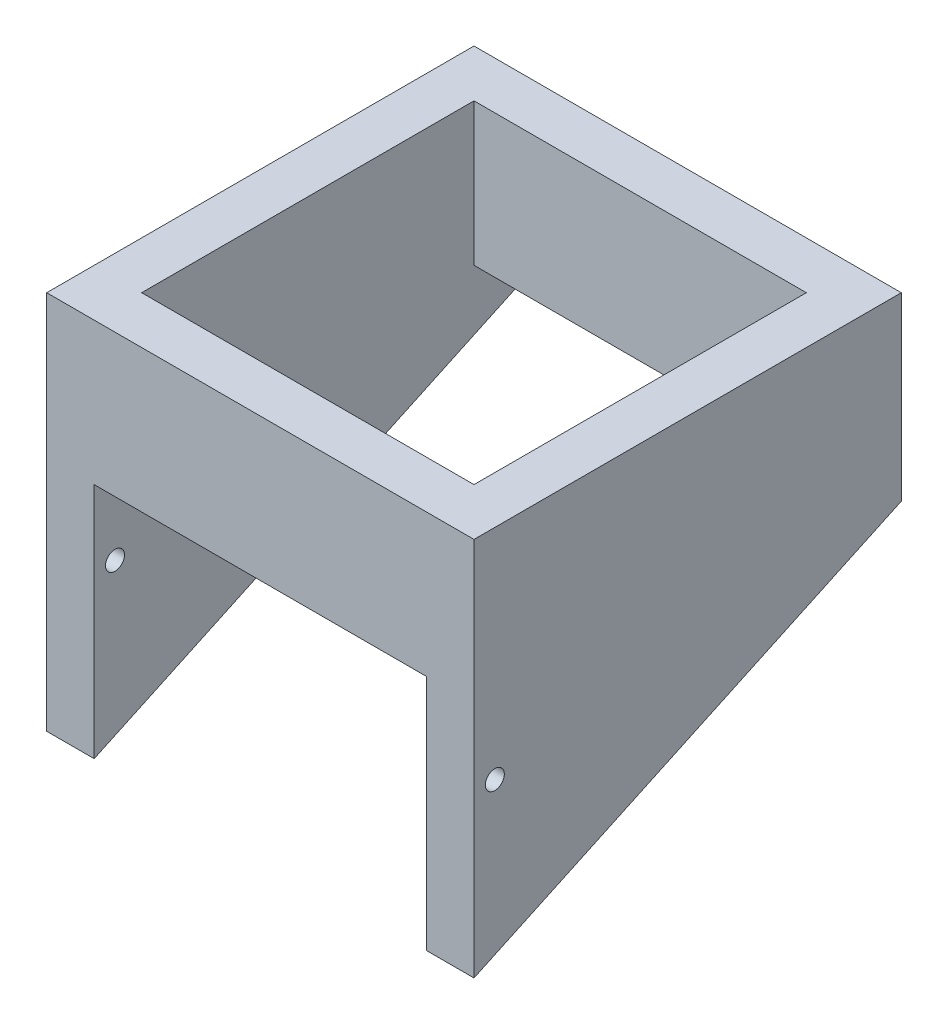
SolidWorks part; units mm, degrees
ref_plane "Alzado" through (0, 0, 0) normal (0, 0, 1) x (1, 0, 0)
ref_plane "Planta" through (0, 0, 0) normal (0, 1, 0) x (1, 0, 0)
ref_plane "Vista lateral" through (0, 0, 0) normal (1, 0, 0) x (0, 0, -1)
sketch "Croquis1" plane through (0, 0, 0) normal (0, 1, 0) x (1, 0, 0)
  line L1 (-22.5, -22.5) -> (22.5, -22.5)
  line L2 (-22.5, -22.5) -> (-22.5, 22.5)
  line L3 (-22.5, 22.5) -> (22.5, 22.5)
  line L4 (22.5, -22.5) -> (22.5, 22.5)
  line L5 (-22.5, -22.5) -> (22.5, 22.5) construction
  line L6 (-22.5, 22.5) -> (22.5, -22.5) construction
  line L7 (-17.5, -17.5) -> (17.5, -17.5)
  line L8 (-17.5, -17.5) -> (-17.5, 17.5)
  line L9 (-17.5, 17.5) -> (17.5, 17.5)
  line L10 (17.5, -17.5) -> (17.5, 17.5)
  line L11 (-17.5, -17.5) -> (17.5, 17.5) construction
  line L12 (-17.5, 17.5) -> (17.5, -17.5) construction
  point P0 (0, 0)
  point P6 (0, 0)
  dimension "D1" = 45
  dimension "D2" = 45
  dimension "D3" = 35
  dimension "D4" = 35
extrude "Saliente-Extruir1" add sketch "Croquis1" along normal mid plane 40
sketch "Croquis3" plane through (22.5, 0, 0) normal (1, 0, 0) x (0, 0, -1)
  line L0 (-22.5, -20) -> (22.5, -20)
  line L1 (22.5, -20) -> (22.5, 0.9838)
  line L2 (22.5, 20) -> (22.5, -20) construction
  line L3 (22.5, 0.9838) -> (-22.5, -20)
  dimension "D1" = 25
extrude "Cortar-Extruir1" cut sketch "Croquis3" against normal through all
sketch "Croquis6" plane through (0, 0, 22.5) normal (0, 0, 1) x (1, 0, 0)
  line L0 (-22.5, -20) -> (22.5, -20) construction
  line L1 (-17.5, -20) -> (17.5, -20)
  line L2 (-17.5, -20) -> (-17.5, 5)
  line L3 (-17.5, 5) -> (17.5, 5)
  line L4 (17.5, -20) -> (17.5, 5)
  line L5 (22.5, 20) -> (22.5, -20) construction
  line L6 (-22.5, 20) -> (-22.5, -20) construction
  dimension "D1" = 5
  dimension "D2" = 5
  dimension "D3" = 25
extrude "Cortar-Extruir2" cut sketch "Croquis6" against normal through all contours L3 L4 L1 L2
sketch "Croquis7" plane through (22.5, 0, 0) normal (1, 0, 0) x (0, 0, -1)
  circle A0 centre (-20.3076, -3) radius 1
  dimension "D1" = 2
  dimension "D2" = 17
extrude "Cortar-Extruir3" cut sketch "Croquis7" against normal through all
